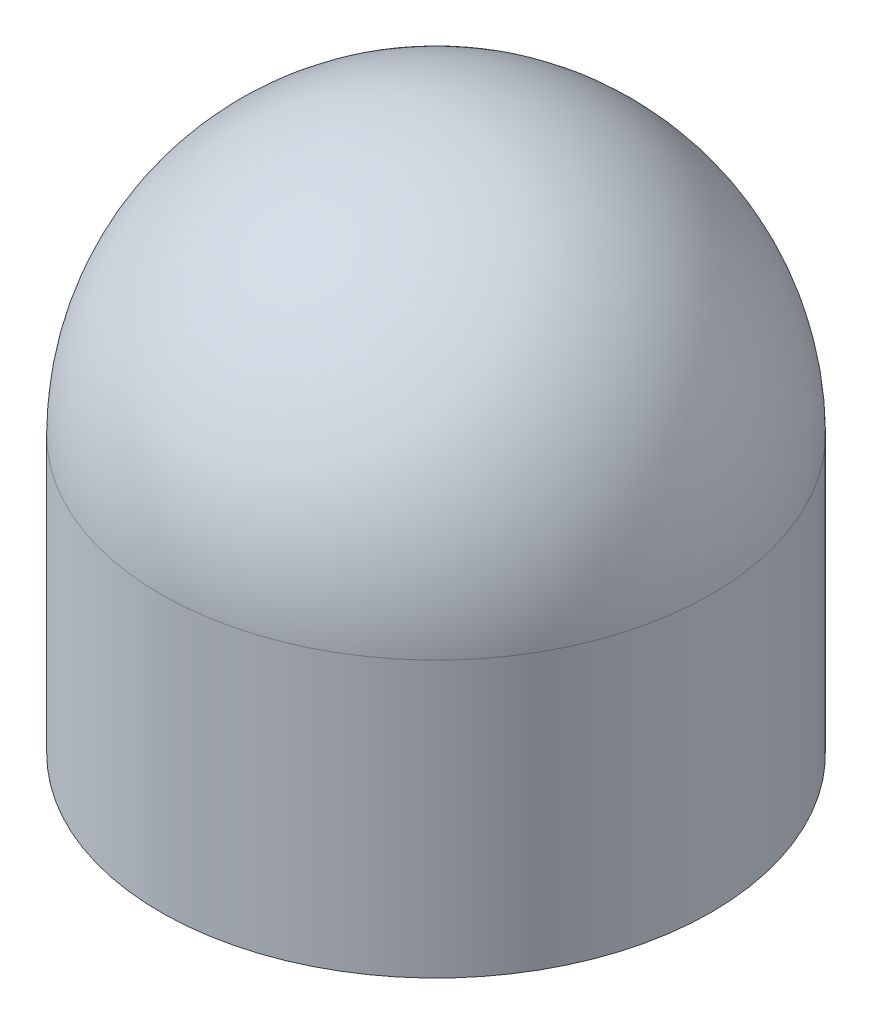
SolidWorks part; units mm, degrees
material "Polyester Resin"
ref_plane "Front Plane" through (0, 0, 0) normal (0, 0, 1) x (1, 0, 0)
ref_plane "Top Plane" through (0, 0, 0) normal (0, 1, 0) x (1, 0, 0)
ref_plane "Right Plane" through (0, 0, 0) normal (1, 0, 0) x (0, 0, -1)
sketch "Sketch1" plane through (0, 0, 0) normal (0, 0, 1) x (1, 0, 0)
  line L0 (0, 0) -> (40, 0)
  line L3 (0, 0) -> (0, 80)
  line L4 (0, 40) -> (40, 40) construction
  line L25 (40, 40) -> (40, 0) construction
  line L29 (40, 40) -> (40, 0)
  arc A0 (40, 40) -> (0, 80) centre (0, 40) ccw
  point P4 (0, -1.5337)
  dimension "D1" = 40
  dimension "D2" = 40
revolve "Revolve1" add sketch "Sketch1" angle 360 about L3
equation "\"d\"= 80mm"
equation "\"h\"= \"d\" / 2"
equation "\"D1@Sketch1\"=\"d\"/2"
equation "\"D2@Sketch1\"=\"h\""
